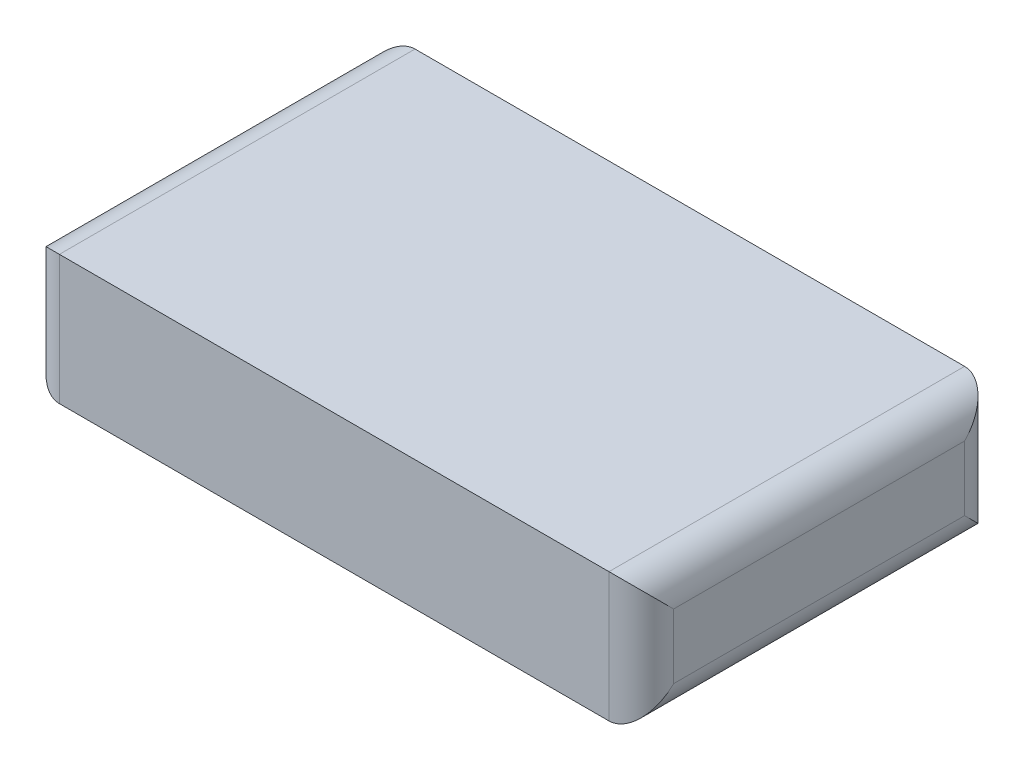
SolidWorks part; units mm, degrees
ref_plane "前视基准面" through (0, 0, 0) normal (0, 0, 1) x (1, 0, 0)
ref_plane "上视基准面" through (0, 0, 0) normal (0, 1, 0) x (1, 0, 0)
ref_plane "右视基准面" through (0, 0, 0) normal (1, 0, 0) x (0, 0, -1)
sketch "草图1" plane through (0, 0, 0) normal (0, 1, 0) x (1, 0, 0)
  line L1 (-18, 6.7031) -> (1, 6.7031)
  line L2 (-18, 6.7031) -> (-18, -4.2969)
  line L3 (-18, -4.2969) -> (1, -4.2969)
  line L4 (1, 6.7031) -> (1, -4.2969)
  line L5 (-18, 6.7031) -> (1, -4.2969) construction
  line L6 (-18, -4.2969) -> (1, 6.7031) construction
  point P0 (-8.5, 1.2031)
  dimension "D1" = 19
  dimension "D2" = 11
extrude "凸台-拉伸1" add sketch "草图1" along normal blind 4
fillet "圆角1" radius 1 8 edges at (1, 2, 4.2969) (1, 4, -1.2031) (1, 2, -6.7031) (1, 0, -1.2031) (-18, 2, -6.7031) (-18, 4, -1.2031) (-18, 2, 4.2969) (-18, 0, -1.2031)
